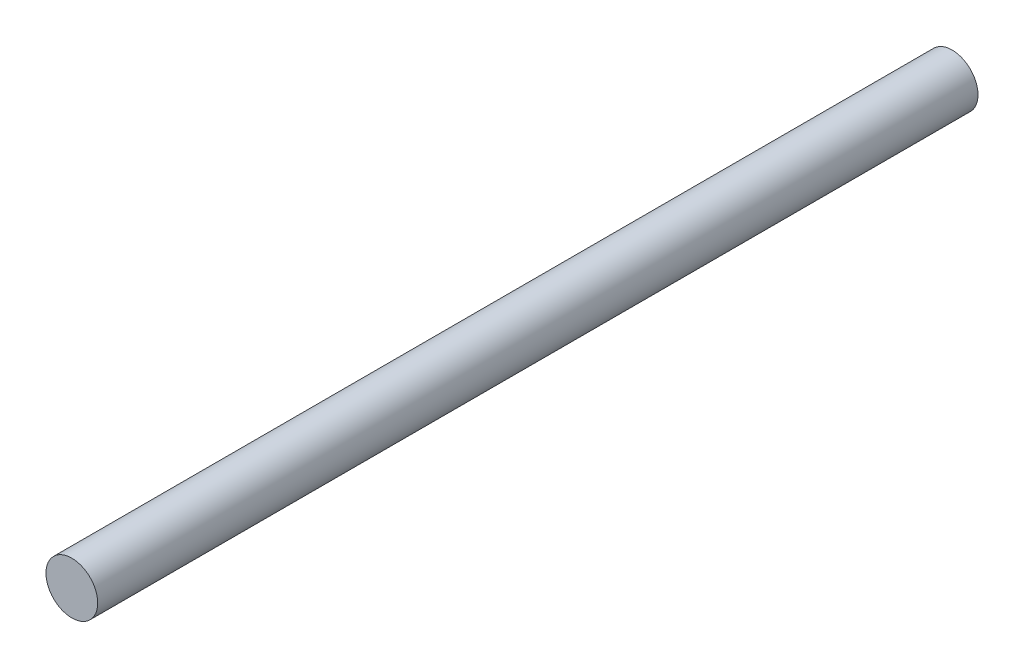
SolidWorks part; units mm, degrees
ref_plane "Front Plane" through (0, 0, 0) normal (0, 0, 1) x (1, 0, 0)
ref_plane "Top Plane" through (0, 0, 0) normal (0, 1, 0) x (1, 0, 0)
ref_plane "Right Plane" through (0, 0, 0) normal (1, 0, 0) x (0, 0, -1)
sketch "Sketch1" plane through (0, 0, 0) normal (0, 0, 1) x (1, 0, 0)
  circle A0 centre (0, 0) radius 5
extrude "Boss-Extrude1" add sketch "Sketch1" along normal blind 170
